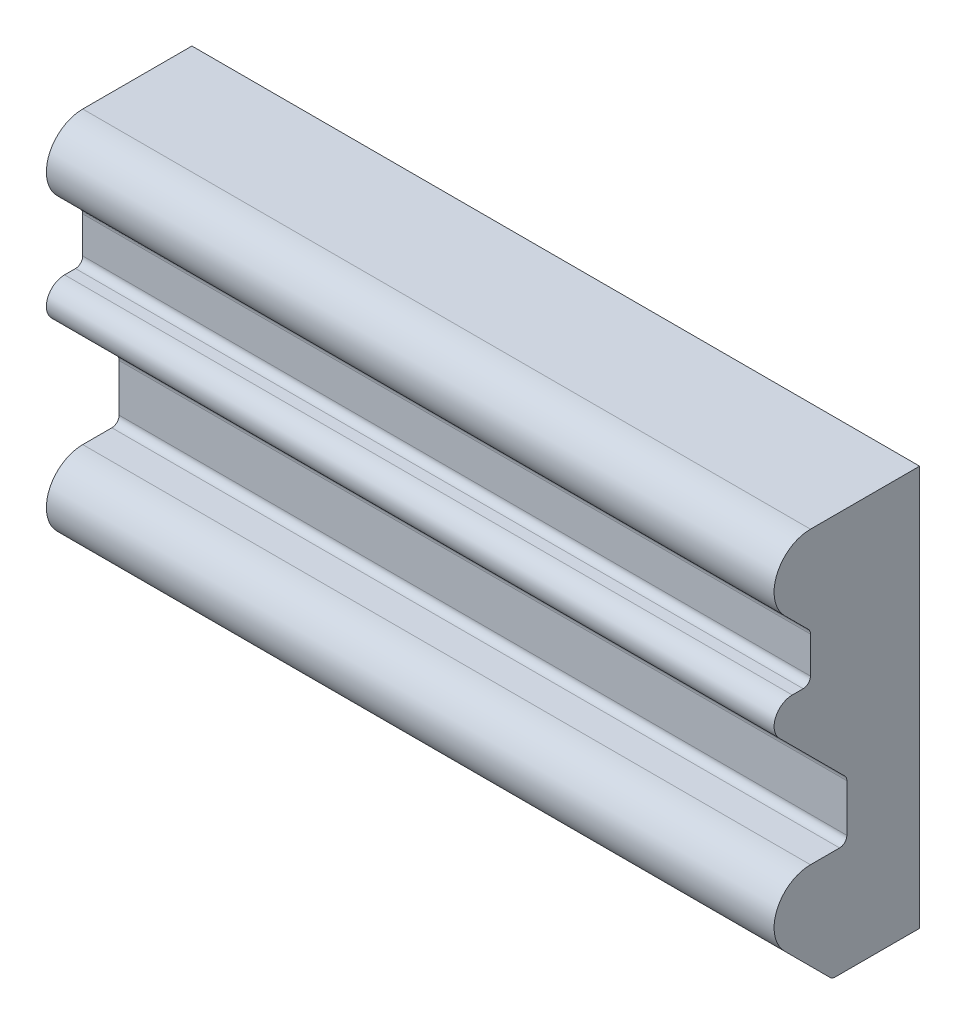
SolidWorks part; units mm, degrees
ref_plane "Front" through (0, 0, 0) normal (0, 0, 1) x (1, 0, 0)
ref_plane "Top" through (0, 0, 0) normal (0, 1, 0) x (1, 0, 0)
ref_plane "Right" through (0, 0, 0) normal (1, 0, 0) x (0, 0, -1)
sketch "Croquis1" plane through (0, 0, 0) normal (1, 0, 0) x (0, 0, -1)
  line L1 (0, 0) -> (-23.1838, 0)
  line L2 (0, 0) -> (0, 110)
  line L3 (0, 110) -> (-30, 110)
  line L5 (-35, 73.0294) -> (-32, 73.0294)
  line L10 (-30, 85.0294) -> (-30, 75.0294)
  line L14 (-20, 32.1299) -> (-20, 45.1299)
  line L16 (-38.5355, 64.4939) -> (-20.5858, 46.5442)
  line L17 (-30, 30.1299) -> (-22, 30.1299)
  line L18 (-37.0711, 92.9289) -> (-30.5858, 86.4437)
  line L19 (-37.0711, 13.0589) -> (-24.598, 0.5858)
  line L20 (-38.5355, 64.4939) -> (-38.5355, 40.8589) construction
  line L21 (-37.0711, 13.0589) -> (-37.0711, -11.1187) construction
  line L22 (-37.0711, 92.9289) -> (-37.0711, 73.2763) construction
  arc A2 (-30, 110) -> (-37.0711, 92.9289) centre (-30, 100) ccw
  arc A3 (-30, 30.1299) -> (-37.0711, 13.0589) centre (-30, 20.1299) ccw
  arc A6 (-35, 73.0294) -> (-38.5355, 64.4939) centre (-35, 68.0294) ccw
  arc A8 (-30.5858, 86.4437) -> (-30, 85.0294) centre (-32, 85.0294) cw
  arc A9 (-30, 75.0294) -> (-32, 73.0294) centre (-32, 75.0294) cw
  arc A10 (-20.5858, 46.5442) -> (-20, 45.1299) centre (-22, 45.1299) cw
  arc A11 (-20, 32.1299) -> (-22, 30.1299) centre (-22, 32.1299) cw
  arc A12 (-23.1838, 0) -> (-24.598, 0.5858) centre (-23.1838, 2) cw
  point P0 (0, 0)
  point P11 (-30, 73.0294)
  point P31 (-24.2661, 18.0351)
  point P33 (0, 0)
  dimension "D1" = 2
  dimension "D2" = 10
  dimension "D8" = 5
  dimension "D9" = 45
  dimension "D12" = 2
  dimension "D7" = 2
  dimension "D10" = 2
  dimension "D11" = 2
  dimension "D16" = 40
  dimension "D3" = 40
  dimension "D4" = 45
  dimension "D5" = 10
  dimension "D6" = 20
  dimension "D13" = 45
  dimension "D14" = 110
  dimension "D15" = 40
  dimension "D17" = 12
  dimension "D18" = 15
extrude "Saliente-Extruir1" add sketch "Croquis1" along normal blind 200
